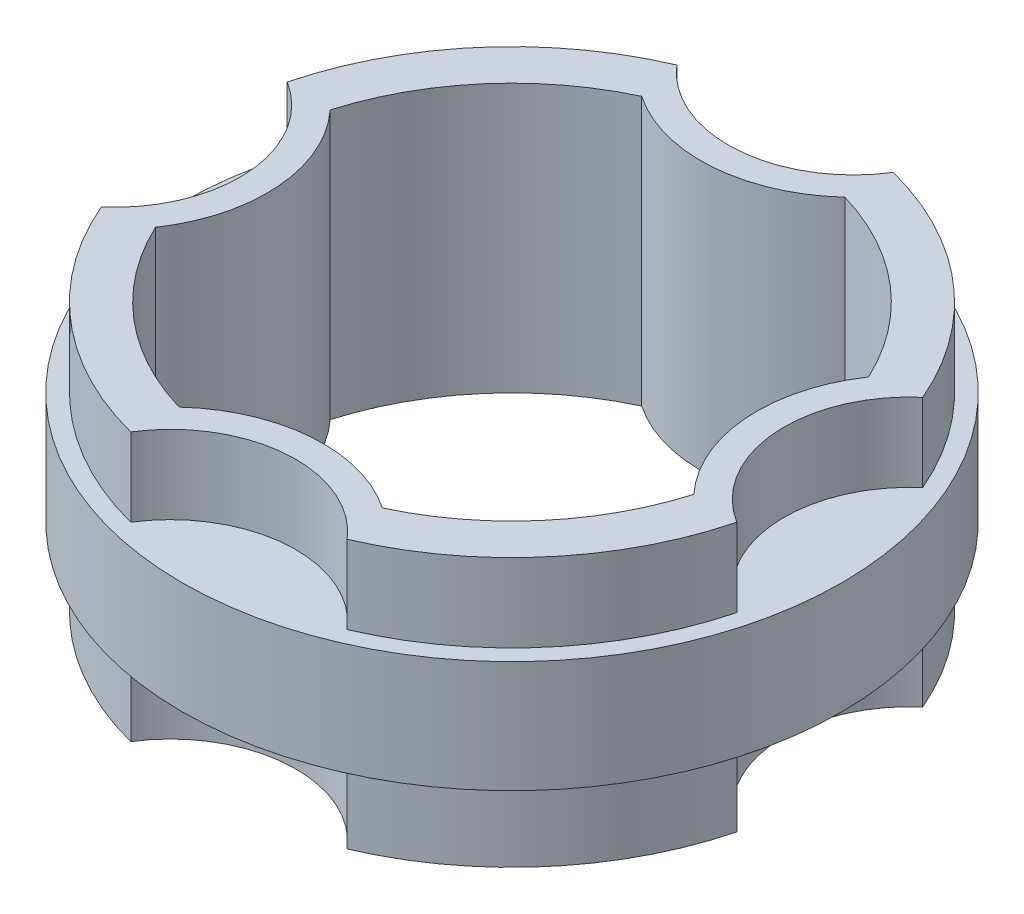
SolidWorks part; units mm, degrees
ref_plane "Front Plane" through (0, 0, 0) normal (0, 0, 1) x (1, 0, 0)
ref_plane "Top Plane" through (0, 0, 0) normal (0, 1, 0) x (1, 0, 0)
ref_plane "Right Plane" through (0, 0, 0) normal (1, 0, 0) x (0, 0, -1)
sketch "Sketch1" plane through (0, 0, 0) normal (0, 1, 0) x (1, 0, 0)
  circle A0 centre (0, 0) radius 76.2
  circle A1 centre (0, 0) radius 88.9
  dimension "D1" = 177.8
  dimension "D2" = 152.4
extrude "Boss-Extrude1" add sketch "Sketch1" along normal mid plane 76.2
sketch "Sketch2" plane through (0, 0, 0) normal (0, 1, 0) x (1, 0, 0)
  circle A0 centre (0, 0) radius 76.2
  circle A1 centre (0, 0) radius 93.6625
  dimension "D1" = 152.4
  dimension "D2" = 187.325
extrude "Boss-Extrude2" add sketch "Sketch2" along normal mid plane 31.75
sketch "Sketch4" plane through (0, 38.1, 0) normal (0, 1, 0) x (1, 0, 0)
  line L0 (93.6625, 0) -> (-93.6625, 0) construction
  line L1 (0, -93.6625) -> (0, 93.6625) construction
  circle A0 centre (0, 0) radius 93.6625 construction
  arc A1 (81.7524, 34.925) -> (86.0771, -22.225) centre (104.9272, 7.9401) ccw
  circle A2 centre (0, 0) radius 88.9 construction
  arc A3 (81.7524, 34.925) -> (86.0771, -22.225) centre (0, 0) cw
  dimension "D1" = 57.15
  dimension "D2" = 22.225
extrude "Cut-Extrude2" cut sketch "Sketch4" against normal up to surface (53.975 mm away)
pattern_circular "CirPattern3" count 4 over 360 about axis through (0, 0, 0) along (0, 1, 0) of "Cut-Extrude2"
mirror "Mirror4" about plane through (0, 0, 0) normal (0, 1, 0) of "CirPattern3", "Cut-Extrude2"
sketch "Sketch7" plane through (0, 0, 0) normal (0, 1, 0) x (1, 0, 0)
  circle A0 centre (0, 0) radius 88.9
  circle A1 centre (0, 0) radius 76.2
extrude "Boss-Extrude5" add sketch "Sketch7" along normal mid plane 31.75
sketch "Sketch8" plane through (0, 0, 0) normal (0, 1, 0) x (1, 0, 0)
  arc A1 (34.925, -81.7524) -> (86.0771, -22.225) centre (0, 0) ccw construction
  arc A2 (-81.7524, -34.925) -> (-22.225, -86.0771) centre (0, 0) ccw construction
  arc A3 (42.1066, -78.2959) -> (-29.845, -83.7406) centre (7.9401, -104.9272) ccw
  arc A9 (34.925, -81.7524) -> (22.9282, -72.6687) centre (7.9401, -104.9272) ccw construction
  arc A10 (34.925, -81.7524) -> (-22.225, -86.0771) centre (7.9401, -104.9272) ccw
  arc A11 (34.925, -81.7524) -> (22.9282, -72.6687) centre (7.9401, -104.9272) ccw construction
  arc A12 (42.1066, -78.2959) -> (34.925, -81.7524) centre (0, 0) cw
  arc A13 (-22.225, -86.0771) -> (-29.845, -83.7406) centre (0, 0) cw
extrude "Boss-Extrude6" add sketch "Sketch8" along normal mid plane 76.2
pattern_circular "CirPattern4" count 4 over 360 about axis through (0, 0, 0) along (0, 1, 0) of "Boss-Extrude6"
sketch "Sketch9" plane through (0, 15.875, 0) normal (0, 1, 0) x (1, 0, 0)
  arc A0 (22.9282, -72.6687) -> (-11.7318, -75.2915) centre (7.9401, -104.9272) ccw
  arc A1 (22.9282, -72.6687) -> (-11.7318, -75.2915) centre (0, 0) cw
extrude "Boss-Extrude7" add sketch "Sketch9" against normal up to surface (31.75 mm away) up to face at (0, -15.875, 93.6625)
pattern_circular "CirPattern5" count 4 over 360 about axis through (0, 15.875, 0) along (0, -1, 0) of "Boss-Extrude7"
